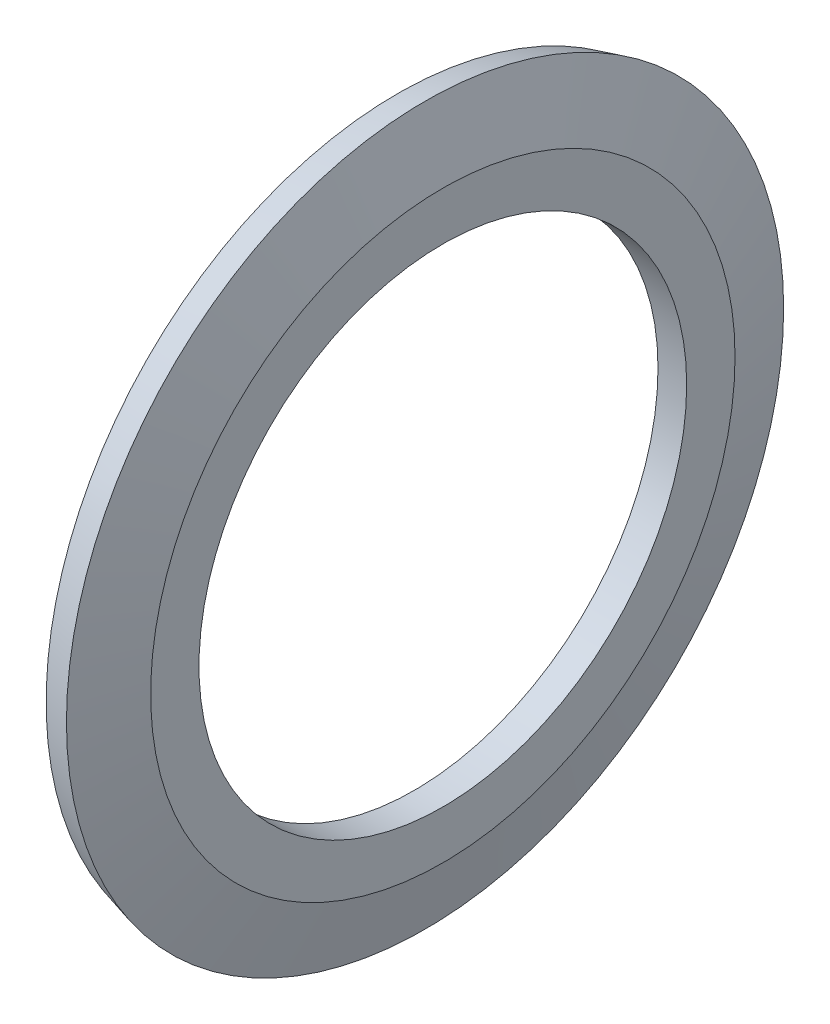
SolidWorks part; units mm, degrees
ref_plane "Front Plane" through (0, 0, 0) normal (0, 0, 1) x (1, 0, 0)
ref_plane "Top Plane" through (0, 0, 0) normal (0, 1, 0) x (1, 0, 0)
ref_plane "Right Plane" through (0, 0, 0) normal (1, 0, 0) x (0, 0, -1)
sketch "Sketch1" plane through (0, 0, 0) normal (0, 0, 1) x (1, 0, 0)
  line L0 (0, 8.5) -> (1, 8.5)
  line L1 (1, 8.5) -> (1, 10.185)
  line L2 (0, 8.5) -> (0, 10.0533)
  line L3 (0, 10.0533) -> (-0.5862, 12.2412)
  line L4 (-0.5862, 12.2412) -> (0.3797, 12.5)
  line L5 (0.3797, 12.5) -> (1, 10.185)
  line L6 (1, 0) -> (0, 0) construction
  dimension "D1" = 15
  dimension "D2" = 1
  dimension "E" = 17
  dimension "P.D." = 20.37
  dimension "F_1" = 25
revolve "Revolve1" add sketch "Sketch1" angle 360 about L6
sketch "Sketch2" [suppressed] plane through (0, 0, 0) normal (0, 0, 1) x (1, 0, 0)
  line L0 (-0.475, 0) -> (0, 0) construction
  line L1 (1, 21) -> (-0.475, 21)
  line L2 (1, 21) -> (1, 20.5)
  line L3 (1, 20.5) -> (-0.475, 20.5)
  line L4 (-0.475, 21) -> (-0.475, 20.5)
  line L5 (-0.475, 20.7412) -> (-0.475, -20.7412) construction
  line L6 (1, -19.1) -> (1, 19.1) construction
  dimension "FC" = 41
revolve "Cut-Revolve1" [suppressed] cut sketch "Sketch2" angle 360 about L0
